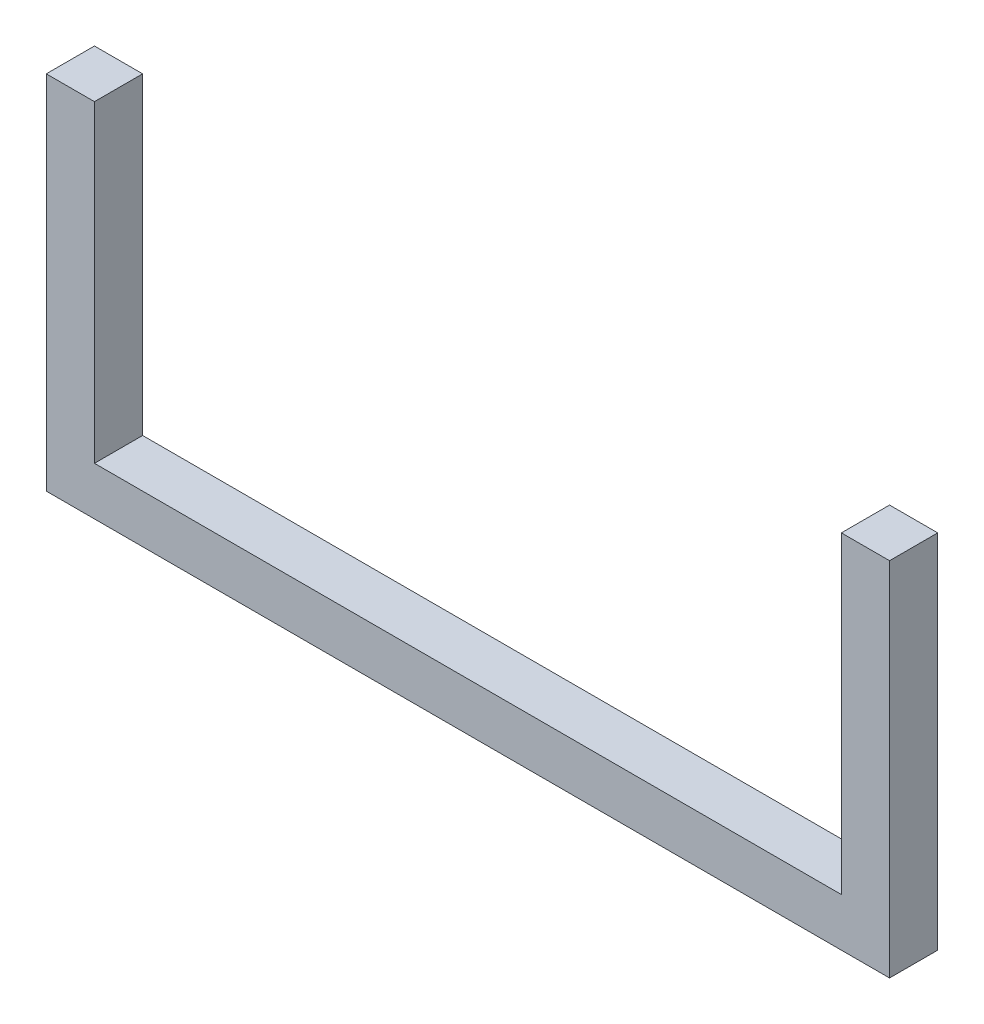
SolidWorks part; units mm, degrees
ref_plane "정면" through (0, 0, 0) normal (0, 0, 1) x (1, 0, 0)
ref_plane "윗면" through (0, 0, 0) normal (0, 1, 0) x (1, 0, 0)
ref_plane "우측면" through (0, 0, 0) normal (1, 0, 0) x (0, 0, -1)
sketch "스케치2" plane through (0, 0, 0) normal (0, 0, 1) x (1, 0, 0)
  line L0 (0, 0) -> (-350, 0)
  line L1 (-350, 0) -> (-350, 150)
  line L2 (-350, 150) -> (-330, 150)
  line L3 (-330, 150) -> (-330, 20)
  line L4 (-330, 20) -> (-20, 20)
  line L5 (-20, 20) -> (-20, 150)
  line L6 (-20, 150) -> (0, 150)
  line L7 (0, 150) -> (0, 0)
  dimension "D1" = 350
  dimension "D2" = 150
  dimension "D3" = 20
  dimension "D4" = 20
  dimension "D5" = 20
  dimension "D6" = 150
extrude "보스-돌출1" add sketch "스케치2" along normal blind 20
